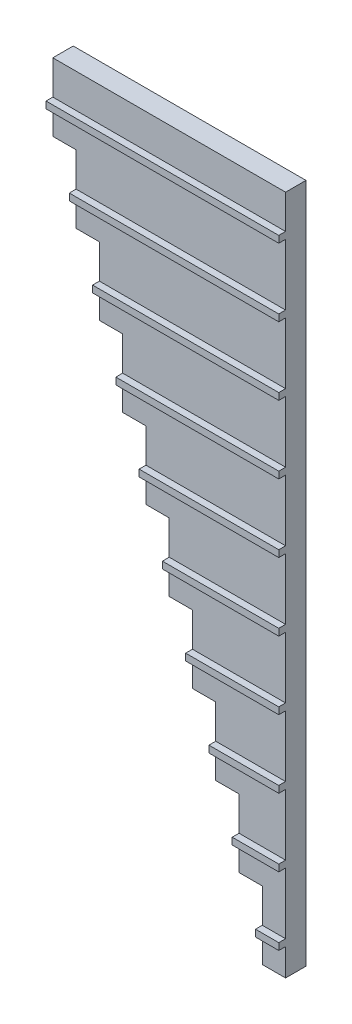
SolidWorks part; units mm, degrees
ref_plane "Front Plane" through (0, 0, 0) normal (0, 0, 1) x (1, 0, 0)
ref_plane "Top Plane" through (0, 0, 0) normal (0, 1, 0) x (1, 0, 0)
ref_plane "Right Plane" through (0, 0, 0) normal (1, 0, 0) x (0, 0, -1)
sketch "Sketch1" plane through (0, 0, 0) normal (0, 0, 1) x (1, 0, 0)
  line L2 (3.2279, -0.7109) -> (3.2279, -10.7109)
  line L3 (3.2279, -10.7109) -> (6.6479, -10.7109)
  line L4 (6.6479, -0.7109) -> (6.6479, -10.7109)
  line L11 (6.6479, 9.2891) -> (6.6479, -0.7109)
  line L15 (6.6479, 19.2891) -> (6.6479, 9.2891)
  line L19 (6.6479, 29.2891) -> (6.6479, 19.2891)
  line L23 (6.6479, 39.2891) -> (6.6479, 29.2891)
  line L27 (6.6479, 49.2891) -> (6.6479, 39.2891)
  line L31 (6.6479, 59.2891) -> (6.6479, 49.2891)
  line L35 (6.6479, 69.2891) -> (6.6479, 59.2891)
  line L39 (6.6479, 79.2891) -> (6.6479, 69.2891)
  line L40 (3.2279, 89.2891) -> (6.6479, 89.2891)
  line L43 (6.6479, 89.2891) -> (6.6479, 79.2891)
  line L44 (-0.1921, -0.7109) -> (3.2279, -0.7109)
  line L47 (3.2279, -0.7109) -> (3.2279, -10.7109)
  line L49 (-0.1921, 9.2891) -> (-0.1921, -0.7109)
  line L50 (-0.1921, -0.7109) -> (3.2279, -0.7109)
  line L80 (-0.1921, 89.2891) -> (3.2279, 89.2891)
  line L88 (-3.6121, 9.2891) -> (-0.1921, 9.2891)
  line L91 (-0.1921, 9.2891) -> (-0.1921, -0.7109)
  line L93 (-3.6121, 19.2891) -> (-3.6121, 9.2891)
  line L94 (-3.6121, 9.2891) -> (-0.1921, 9.2891)
  line L120 (-3.6121, 89.2891) -> (-0.1921, 89.2891)
  line L132 (-7.0321, 19.2891) -> (-3.6121, 19.2891)
  line L135 (-3.6121, 19.2891) -> (-3.6121, 9.2891)
  line L137 (-7.0321, 29.2891) -> (-7.0321, 19.2891)
  line L138 (-7.0321, 19.2891) -> (-3.6121, 19.2891)
  line L160 (-7.0321, 89.2891) -> (-3.6121, 89.2891)
  line L176 (-10.4521, 29.2891) -> (-7.0321, 29.2891)
  line L179 (-7.0321, 29.2891) -> (-7.0321, 19.2891)
  line L181 (-10.4521, 39.2891) -> (-10.4521, 29.2891)
  line L182 (-10.4521, 29.2891) -> (-7.0321, 29.2891)
  line L200 (-10.4521, 89.2891) -> (-7.0321, 89.2891)
  line L220 (-13.8721, 39.2891) -> (-10.4521, 39.2891)
  line L223 (-10.4521, 39.2891) -> (-10.4521, 29.2891)
  line L225 (-13.8721, 49.2891) -> (-13.8721, 39.2891)
  line L226 (-13.8721, 39.2891) -> (-10.4521, 39.2891)
  line L240 (-13.8721, 89.2891) -> (-10.4521, 89.2891)
  line L264 (-17.2921, 49.2891) -> (-13.8721, 49.2891)
  line L267 (-13.8721, 49.2891) -> (-13.8721, 39.2891)
  line L269 (-17.2921, 59.2891) -> (-17.2921, 49.2891)
  line L270 (-17.2921, 49.2891) -> (-13.8721, 49.2891)
  line L280 (-17.2921, 89.2891) -> (-13.8721, 89.2891)
  line L308 (-20.7121, 59.2891) -> (-17.2921, 59.2891)
  line L311 (-17.2921, 59.2891) -> (-17.2921, 49.2891)
  line L313 (-20.7121, 69.2891) -> (-20.7121, 59.2891)
  line L314 (-20.7121, 59.2891) -> (-17.2921, 59.2891)
  line L320 (-20.7121, 89.2891) -> (-17.2921, 89.2891)
  line L352 (-24.1321, 69.2891) -> (-20.7121, 69.2891)
  line L355 (-20.7121, 69.2891) -> (-20.7121, 59.2891)
  line L357 (-24.1321, 79.2891) -> (-24.1321, 69.2891)
  line L358 (-24.1321, 69.2891) -> (-20.7121, 69.2891)
  line L360 (-24.1321, 89.2891) -> (-20.7121, 89.2891)
  line L396 (-27.5521, 79.2891) -> (-24.1321, 79.2891)
  line L399 (-24.1321, 79.2891) -> (-24.1321, 69.2891)
  line L400 (-27.5521, 89.2891) -> (-24.1321, 89.2891)
  line L401 (-27.5521, 89.2891) -> (-27.5521, 79.2891)
  line L402 (-27.5521, 79.2891) -> (-24.1321, 79.2891)
  line L407 (-24.1321, 69.2891) -> (-24.1321, 59.2891) [skipped]
  line L419 (-20.7121, 19.2891) -> (-20.7121, 9.2891) [skipped]
  line L423 (-17.2921, 9.2891) -> (-17.2921, -0.7109) [skipped]
  line L427 (-13.8721, -0.7109) -> (-13.8721, -10.7109) [skipped]
  line L428 (-13.8721, -0.7109) -> (-13.8721, -10.7109) [skipped]
  line L429 (-10.4521, -0.7109) -> (-10.4521, -10.7109) [skipped]
  line L430 (-10.4521, -0.7109) -> (-10.4521, -10.7109) [skipped]
  line L431 (-7.0321, -0.7109) -> (-7.0321, -10.7109) [skipped]
  line L432 (-7.0321, -0.7109) -> (-7.0321, -10.7109) [skipped]
  line L433 (-7.0321, -10.7109) -> (-3.6121, -10.7109) [skipped]
  line L434 (-3.6121, -10.7109) -> (-0.1921, -10.7109) [skipped]
  line L435 (-0.1921, -0.7109) -> (-0.1921, -10.7109) [skipped]
  line L436 (-0.1921, -0.7109) -> (-0.1921, -10.7109) [skipped]
  line L440 (-3.6121, 9.2891) -> (-3.6121, -0.7109) [skipped]
  line L444 (-7.0321, 19.2891) -> (-7.0321, 9.2891) [skipped]
  line L448 (-10.4521, 29.2891) -> (-10.4521, 19.2891) [skipped]
  line L452 (-13.8721, 39.2891) -> (-13.8721, 29.2891) [skipped]
  line L456 (-17.2921, 49.2891) -> (-17.2921, 39.2891) [skipped]
  line L460 (-20.7121, 59.2891) -> (-20.7121, 49.2891) [skipped]
  line L462 (-24.1321, 59.2891) -> (-24.1321, 49.2891) [skipped]
  line L467 (-20.7121, 49.2891) -> (-20.7121, 39.2891) [skipped]
  line L473 (-17.2921, 29.2891) -> (-17.2921, 19.2891) [skipped]
  line L477 (-13.8721, 19.2891) -> (-13.8721, 9.2891) [skipped]
  line L483 (-10.4521, -10.7109) -> (-7.0321, -10.7109) [skipped]
  line L484 (-3.6121, -0.7109) -> (-3.6121, -10.7109) [skipped]
  line L485 (-3.6121, -0.7109) -> (-3.6121, -10.7109) [skipped]
  line L489 (-7.0321, 9.2891) -> (-7.0321, -0.7109) [skipped]
  line L491 (-10.4521, 9.2891) -> (-10.4521, -0.7109) [skipped]
  line L492 (-17.2921, 39.2891) -> (-17.2921, 29.2891) [skipped]
  line L496 (-13.8721, 29.2891) -> (-13.8721, 19.2891) [skipped]
  line L500 (-10.4521, 19.2891) -> (-10.4521, 9.2891) [skipped]
  line L504 (-20.7121, 39.2891) -> (-20.7121, 29.2891) [skipped]
  line L506 (-24.1321, 39.2891) -> (-24.1321, 29.2891) [skipped]
  line L511 (-24.1321, 49.2891) -> (-24.1321, 39.2891) [skipped]
  line L514 (-24.1321, 29.2891) -> (-24.1321, 19.2891) [skipped]
  line L519 (-24.1321, 9.2891) -> (-24.1321, -0.7109) [skipped]
  line L525 (-20.7121, 9.2891) -> (-20.7121, -0.7109) [skipped]
  line L527 (-24.1321, -0.7109) -> (-24.1321, -10.7109) [skipped]
  line L528 (-24.1321, -0.7109) -> (-24.1321, -10.7109) [skipped]
  line L529 (-27.5521, -10.7109) -> (-24.1321, -10.7109) [skipped]
  line L530 (-24.1321, -10.7109) -> (-20.7121, -10.7109) [skipped]
  line L531 (-20.7121, -10.7109) -> (-17.2921, -10.7109) [skipped]
  line L538 (-20.7121, 29.2891) -> (-20.7121, 19.2891) [skipped]
  line L539 (-17.2921, 19.2891) -> (-17.2921, 9.2891) [skipped]
  line L542 (-24.1321, 19.2891) -> (-24.1321, 9.2891) [skipped]
  line L548 (-13.8721, 9.2891) -> (-13.8721, -0.7109) [skipped]
  line L553 (-17.2921, -10.7109) -> (-13.8721, -10.7109) [skipped]
  line L554 (-13.8721, -10.7109) -> (-10.4521, -10.7109) [skipped]
  line L555 (-17.2921, -0.7109) -> (-17.2921, -10.7109) [skipped]
  line L556 (-17.2921, -0.7109) -> (-17.2921, -10.7109) [skipped]
  line L557 (-20.7121, -0.7109) -> (-20.7121, -10.7109) [skipped]
  line L558 (-20.7121, -0.7109) -> (-20.7121, -10.7109) [skipped]
  line L561 (-27.5521, -0.7109) -> (-27.5521, -10.7109) [skipped]
  line L565 (-0.1921, -10.7109) -> (3.2279, -10.7109) [skipped]
  line L566 (-24.1321, 89.2891) -> (-24.1321, 79.2891) [skipped]
  line L568 (-20.7121, 89.2891) -> (-20.7121, 79.2891) [skipped]
  line L570 (-17.2921, 89.2891) -> (-17.2921, 79.2891) [skipped]
  line L572 (-13.8721, 89.2891) -> (-13.8721, 79.2891) [skipped]
  line L574 (-10.4521, 89.2891) -> (-10.4521, 79.2891) [skipped]
  line L576 (-7.0321, 89.2891) -> (-7.0321, 79.2891) [skipped]
  line L578 (-3.6121, 89.2891) -> (-3.6121, 79.2891) [skipped]
  line L580 (-0.1921, 89.2891) -> (-0.1921, 79.2891) [skipped]
  line L582 (3.2279, 89.2891) -> (3.2279, 79.2891) [skipped]
  line L583 (3.2279, 89.2891) -> (3.2279, 79.2891) [skipped]
  line L585 (3.2279, 79.2891) -> (6.6479, 79.2891) [skipped]
  line L587 (3.2279, 69.2891) -> (6.6479, 69.2891) [skipped]
  line L588 (3.2279, 59.2891) -> (6.6479, 59.2891) [skipped]
  line L591 (3.2279, 49.2891) -> (6.6479, 49.2891) [skipped]
  line L592 (3.2279, 49.2891) -> (3.2279, 39.2891) [skipped]
  line L593 (3.2279, 49.2891) -> (3.2279, 39.2891) [skipped]
  line L594 (-0.1921, 49.2891) -> (-0.1921, 39.2891) [skipped]
  line L595 (-3.6121, 49.2891) -> (-3.6121, 39.2891) [skipped]
  line L596 (-7.0321, 49.2891) -> (-7.0321, 39.2891) [skipped]
  line L597 (-10.4521, 49.2891) -> (-10.4521, 39.2891) [skipped]
  line L599 (-13.8721, 59.2891) -> (-13.8721, 49.2891) [skipped]
  line L601 (-17.2921, 69.2891) -> (-17.2921, 59.2891) [skipped]
  line L603 (-20.7121, 79.2891) -> (-20.7121, 69.2891) [skipped]
  line L604 (-7.0321, 79.2891) -> (-7.0321, 69.2891) [skipped]
  line L607 (-0.1921, 79.2891) -> (-0.1921, 69.2891) [skipped]
  line L609 (-3.6121, 79.2891) -> (-3.6121, 69.2891) [skipped]
  line L611 (-10.4521, 79.2891) -> (-10.4521, 69.2891) [skipped]
  line L613 (-13.8721, 79.2891) -> (-13.8721, 69.2891) [skipped]
  line L615 (-17.2921, 79.2891) -> (-17.2921, 69.2891) [skipped]
  line L616 (-13.8721, 69.2891) -> (-13.8721, 59.2891) [skipped]
  line L618 (-10.4521, 69.2891) -> (-10.4521, 59.2891) [skipped]
  line L620 (-7.0321, 69.2891) -> (-7.0321, 59.2891) [skipped]
  line L622 (-3.6121, 59.2891) -> (-3.6121, 49.2891) [skipped]
  line L624 (-0.1921, 59.2891) -> (-0.1921, 49.2891) [skipped]
  line L626 (3.2279, 79.2891) -> (3.2279, 69.2891) [skipped]
  line L627 (3.2279, 79.2891) -> (3.2279, 69.2891) [skipped]
  line L628 (3.2279, 59.2891) -> (3.2279, 49.2891) [skipped]
  line L629 (3.2279, 59.2891) -> (3.2279, 49.2891) [skipped]
  line L630 (3.2279, 69.2891) -> (3.2279, 59.2891) [skipped]
  line L631 (3.2279, 69.2891) -> (3.2279, 59.2891) [skipped]
  line L632 (-7.0321, 59.2891) -> (-7.0321, 49.2891) [skipped]
  line L633 (-10.4521, 59.2891) -> (-10.4521, 49.2891) [skipped]
  line L634 (-3.6121, 69.2891) -> (-3.6121, 59.2891) [skipped]
  line L635 (-0.1921, 69.2891) -> (-0.1921, 59.2891) [skipped]
  line L638 (-7.0321, 39.2891) -> (-7.0321, 29.2891) [skipped]
  line L640 (-3.6121, 39.2891) -> (-3.6121, 29.2891) [skipped]
  line L642 (-0.1921, 39.2891) -> (-0.1921, 29.2891) [skipped]
  line L644 (3.2279, 39.2891) -> (3.2279, 29.2891) [skipped]
  line L645 (3.2279, 39.2891) -> (3.2279, 29.2891) [skipped]
  line L647 (3.2279, 39.2891) -> (6.6479, 39.2891) [skipped]
  line L653 (-3.6121, 29.2891) -> (-3.6121, 19.2891) [skipped]
  line L654 (-0.1921, 29.2891) -> (-0.1921, 19.2891) [skipped]
  line L659 (-0.1921, 19.2891) -> (-0.1921, 9.2891) [skipped]
  line L663 (3.2279, 9.2891) -> (3.2279, -0.7109) [skipped]
  line L664 (3.2279, 9.2891) -> (3.2279, -0.7109) [skipped]
  line L666 (3.2279, 9.2891) -> (6.6479, 9.2891) [skipped]
  line L668 (3.2279, 19.2891) -> (6.6479, 19.2891) [skipped]
  line L670 (3.2279, 29.2891) -> (6.6479, 29.2891) [skipped]
  line L671 (3.2279, 19.2891) -> (3.2279, 9.2891) [skipped]
  line L672 (3.2279, 19.2891) -> (3.2279, 9.2891) [skipped]
  line L673 (3.2279, 29.2891) -> (3.2279, 19.2891) [skipped]
  line L674 (3.2279, 29.2891) -> (3.2279, 19.2891) [skipped]
  line L675 (3.2279, -0.7109) -> (6.6479, -0.7109) [skipped]
  dimension "D1" = 3.42
  dimension "D2" = 10
  dimension "D3" = 10
  dimension "D4" = 10
extrude "Boss-Extrude2" add sketch "Sketch1" along normal blind 3 contours L400 L401 L396 L357 L352 L313 L308 L269 L264 L225 L220 L181 L176 L137 L132 L93 L88 L49 L44 L2 L3 L4 L11 L15 L19 L23 L27 L31 L35 L39 L43 L40 L80 L120 L160 L200 L240 L280 L320 L360
sketch "Sketch2" plane through (0, 0, 3) normal (0, 0, 1) x (1, 0, 0)
  line L0 (-27.5521, 84.2891) -> (6.6479, 84.2891)
  line L1 (-27.5521, 89.2891) -> (-27.5521, 79.2891) construction
  line L2 (6.6479, 89.2891) -> (6.6479, -10.7109) construction
  line L3 (6.6479, 84.2891) -> (6.6479, 83.2891)
  line L4 (-24.1321, 73.2891) -> (6.6479, 73.2891)
  line L5 (-24.1321, 74.2891) -> (6.6479, 74.2891)
  line L6 (-20.7121, 64.2891) -> (6.6479, 64.2891)
  line L7 (-17.2921, 54.2891) -> (6.6479, 54.2891)
  line L8 (-13.8721, 44.2891) -> (6.6479, 44.2891)
  line L9 (-10.4521, 34.2891) -> (6.6479, 34.2891)
  line L10 (-7.0321, 24.2891) -> (6.6479, 24.2891)
  line L11 (-3.6121, 14.2891) -> (6.6479, 14.2891)
  line L12 (-0.1921, 4.2891) -> (6.6479, 4.2891)
  line L13 (3.2279, -5.7109) -> (6.6479, -5.7109)
  line L14 (-27.5521, 83.2891) -> (6.6479, 83.2891)
  line L15 (-20.7121, 63.2891) -> (6.6479, 63.2891)
  line L16 (-17.2921, 53.2891) -> (6.6479, 53.2891)
  line L17 (-13.8721, 43.2891) -> (6.6479, 43.2891)
  line L18 (-10.4521, 33.2891) -> (6.6479, 33.2891)
  line L19 (-7.0321, 23.2891) -> (6.6479, 23.2891)
  line L20 (-3.6121, 13.2891) -> (6.6479, 13.2891)
  line L21 (-0.1921, 3.2891) -> (6.6479, 3.2891)
  line L22 (3.2279, -6.7109) -> (6.6479, -6.7109)
  line L23 (6.6479, -6.7109) -> (6.6479, -5.7109)
  line L24 (3.2279, -6.7109) -> (3.2279, -5.7109)
  line L26 (-0.1921, 3.2891) -> (-0.1921, 4.2891)
  line L28 (-3.6121, 13.2891) -> (-3.6121, 14.2891)
  line L30 (-7.0321, 23.2891) -> (-7.0321, 24.2891)
  line L32 (-10.4521, 33.2891) -> (-10.4521, 34.2891)
  line L33 (6.6479, 4.2891) -> (6.6479, 3.2891)
  line L34 (-13.8721, 43.2891) -> (-13.8721, 44.2891)
  line L35 (6.6479, 14.2891) -> (6.6479, 13.2891)
  line L36 (-17.2921, 53.2891) -> (-17.2921, 54.2891)
  line L37 (6.6479, 24.2891) -> (6.6479, 23.2891)
  line L38 (-20.7121, 63.2891) -> (-20.7121, 64.2891)
  line L39 (6.6479, 44.2891) -> (6.6479, 43.2891)
  line L40 (-24.1321, 73.2891) -> (-24.1321, 74.2891)
  line L41 (6.6479, 54.2891) -> (6.6479, 53.2891)
  line L42 (-27.5521, 83.2891) -> (-27.5521, 84.2891)
  line L43 (6.6479, 74.2891) -> (6.6479, 73.2891)
  line L44 (6.6479, 64.2891) -> (6.6479, 63.2891)
  line L45 (6.6479, 34.2891) -> (6.6479, 33.2891)
  dimension "D1" = 10
  dimension "D2" = 2
  dimension "D3" = 10
extrude "Boss-Extrude3" add sketch "Sketch2" along normal blind 1
